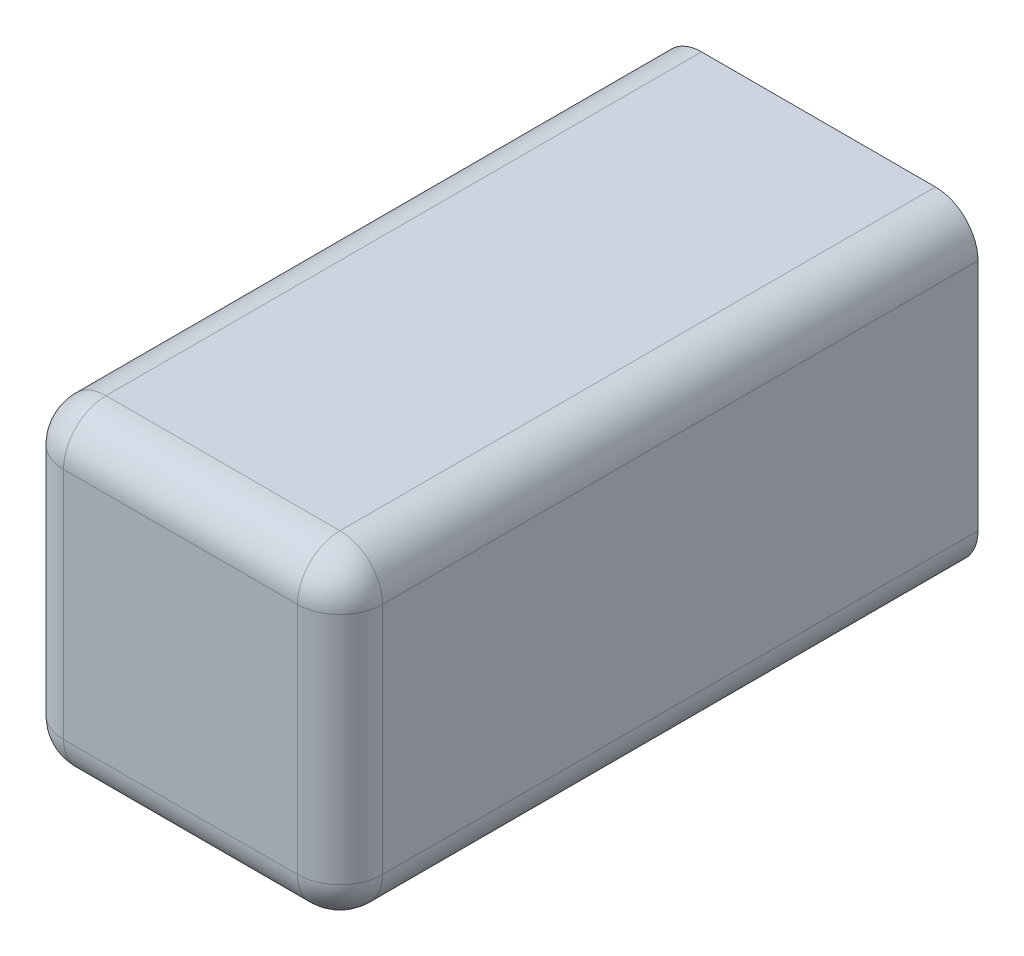
SolidWorks part; units mm, degrees
ref_plane "前视基准面" through (0, 0, 0) normal (0, 0, 1) x (1, 0, 0)
ref_plane "上视基准面" through (0, 0, 0) normal (0, 1, 0) x (1, 0, 0)
ref_plane "右视基准面" through (0, 0, 0) normal (1, 0, 0) x (0, 0, -1)
sketch "草图1" plane through (0, 0, 0) normal (0, 0, 1) x (1, 0, 0)
  line L1 (-7.5, 7.5) -> (7.5, 7.5)
  line L2 (-7.5, 7.5) -> (-7.5, -7.5)
  line L3 (-7.5, -7.5) -> (7.5, -7.5)
  line L4 (7.5, 7.5) -> (7.5, -7.5)
  line L5 (-7.5, 7.5) -> (7.5, -7.5) construction
  line L6 (-7.5, -7.5) -> (7.5, 7.5) construction
  point P0 (0, 0)
  dimension "D1" = 15
  dimension "D2" = 15
extrude "凸台-拉伸1" add sketch "草图1" along normal blind 30
sketch "草图2" plane through (0, 0, 0) normal (0, 0, 1) x (1, 0, 0)
  line L1 (3.5, 3.5) -> (-3.5, 3.5)
  line L2 (3.5, 3.5) -> (3.5, -3.5)
  line L3 (3.5, -3.5) -> (-3.5, -3.5)
  line L4 (-3.5, 3.5) -> (-3.5, -3.5)
  line L5 (3.5, 3.5) -> (-3.5, -3.5) construction
  line L6 (3.5, -3.5) -> (-3.5, 3.5) construction
  point P0 (0, 0)
  dimension "D1" = 7
  dimension "D2" = 7
extrude "切除-拉伸1" cut sketch "草图2" against normal blind 0.001 and the other way blind 25
fillet "圆角1" radius 2 8 edges at (0, 7.5, 30) (7.5, 0, 30) (0, -7.5, 30) (-7.5, 0, 30) (-7.5, -7.5, 15) (7.5, -7.5, 15) (7.5, 7.5, 15) (-7.5, 7.5, 15)
